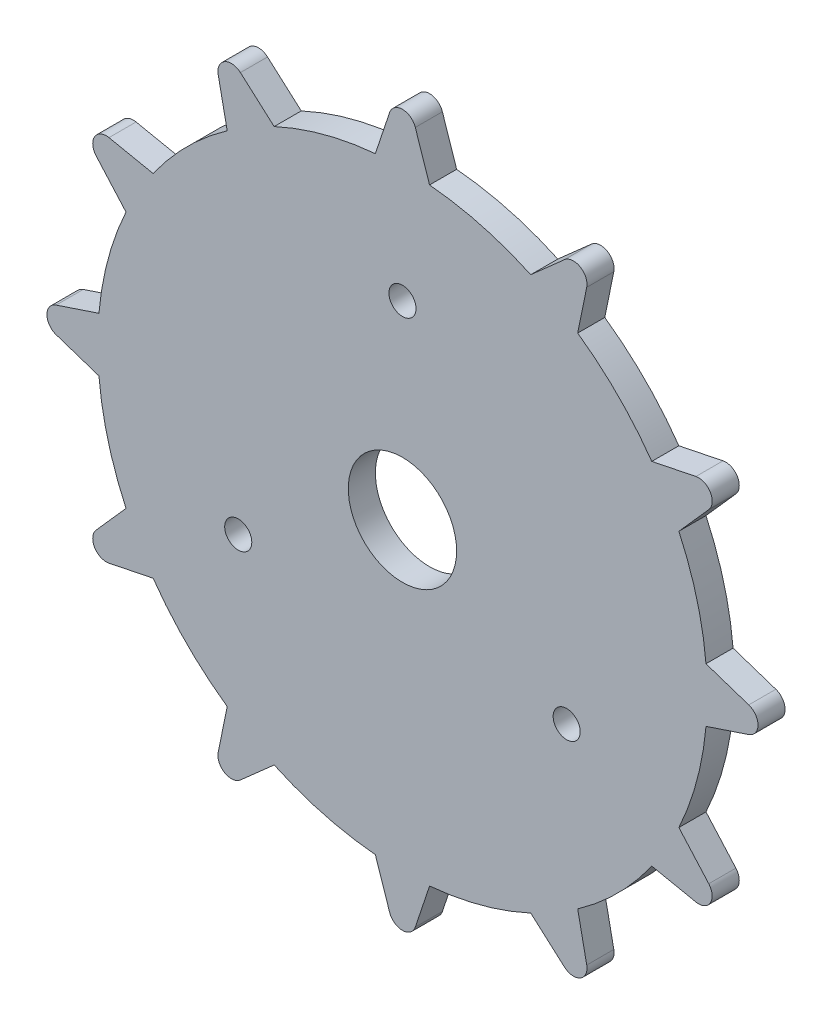
SolidWorks part; units mm, degrees
ref_plane "前视基准面" through (0, 0, 0) normal (0, 0, 1) x (1, 0, 0)
ref_plane "上视基准面" through (0, 0, 0) normal (0, 1, 0) x (1, 0, 0)
ref_plane "右视基准面" through (0, 0, 0) normal (1, 0, 0) x (0, 0, -1)
sketch "草图1" plane through (0, 0, 0) normal (0, 0, 1) x (1, 0, 0)
  circle A0 centre (0, 0) radius 22.5
  dimension "D1" = 45
extrude "凸台-拉伸1" add sketch "草图1" along normal blind 2
sketch "草图2" plane through (0, 0, 0) normal (0, 0, 1) x (1, 0, 0)
  line L1 (0, 28.4109) -> (-2.002, 22.4108)
  line L2 (0, 28.4109) -> (2, 22.4109)
  circle A0 centre (0, 0) radius 22.5 construction
  arc A1 (2, 22.4109) -> (-2.002, 22.4108) centre (0, 0) ccw
  dimension "D3" = 6
extrude "凸台-拉伸2" add sketch "草图2" along normal blind 2
fillet "圆角1" radius 1 1 edges at (0, 28.4109, 1)
pattern_circular "阵列(圆周)1" count 12 over 360 about axis through (0, 0, 0) along (0, 0, 1) of "圆角1", "凸台-拉伸2"
sketch "草图3" plane through (0, 0, 2) normal (0, 0, 1) x (1, 0, 0)
  circle A0 centre (0, 0) radius 4
  dimension "D1" = 8
extrude "切除-拉伸1" cut sketch "草图3" against normal blind 2
sketch "草图4" plane through (0, 0, 2) normal (0, 0, 1) x (1, 0, 0)
  circle A0 centre (0, 14) radius 1
  dimension "D1" = 2
  dimension "D2" = 14
extrude "切除-拉伸2" cut sketch "草图4" against normal blind 2
pattern_circular "阵列(圆周)2" count 3 over 360 about axis through (0, 0, 0) along (0, 0, 1) of "切除-拉伸2"
